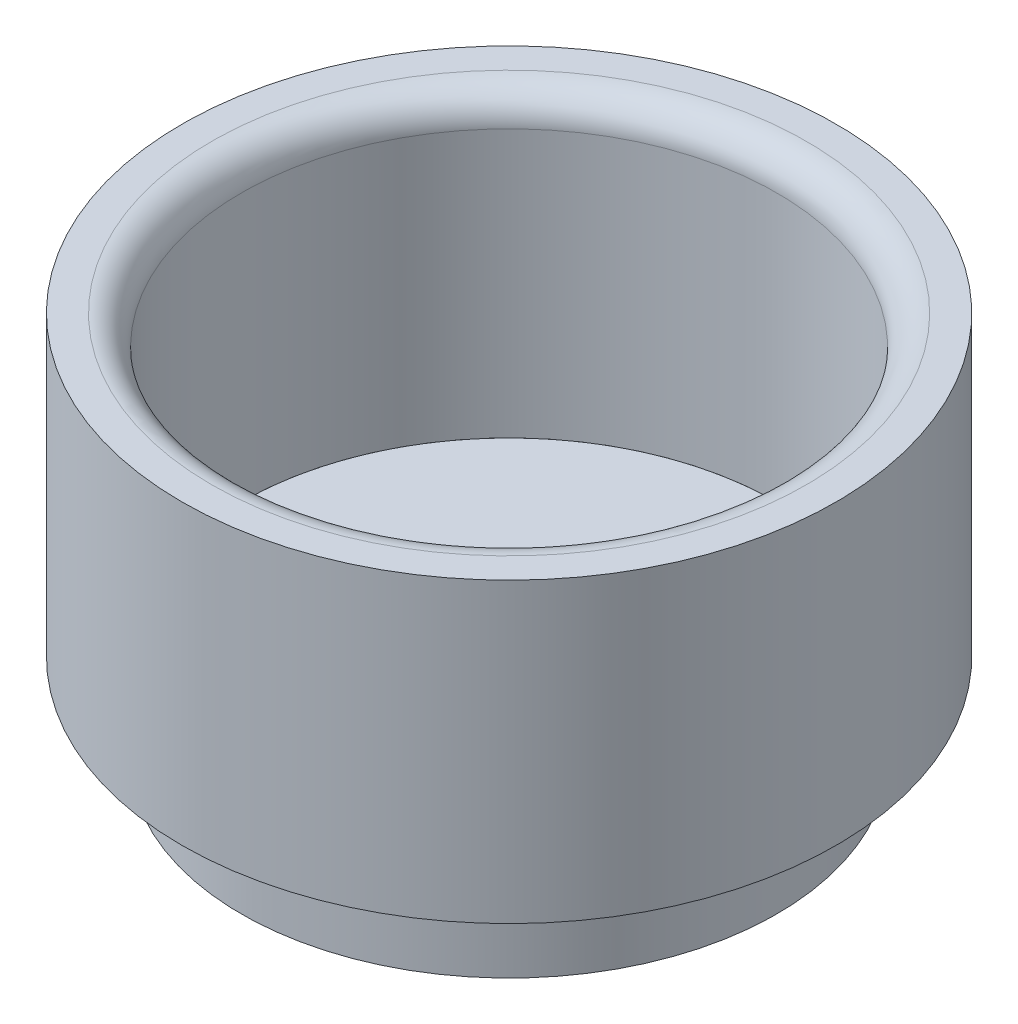
SolidWorks part; units mm, degrees
ref_plane "Front Plane" through (0, 0, 0) normal (0, 0, 1) x (1, 0, 0)
ref_plane "Top Plane" through (0, 0, 0) normal (0, 1, 0) x (1, 0, 0)
ref_plane "Right Plane" through (0, 0, 0) normal (1, 0, 0) x (0, 0, -1)
sketch "Sketch1" plane through (0, 0, 0) normal (0, 1, 0) x (1, 0, 0)
  circle A0 centre (0, 0) radius 9
  circle A1 centre (0, 0) radius 11
  dimension "D1" = 18
  dimension "D2" = 22
extrude "Boss-Extrude1" add sketch "Sketch1" along normal blind 10
fillet "Fillet1" radius 1 1 edges at (0, 10, 9)
sketch "Sketch2" plane through (0, 0, 0) normal (0, -1, 0) x (1, 0, 0)
  circle A0 centre (0, 0) radius 9 construction
  circle A1 centre (0, 0) radius 9
extrude "Boss-Extrude2" add sketch "Sketch2" along normal blind 3 separate body
